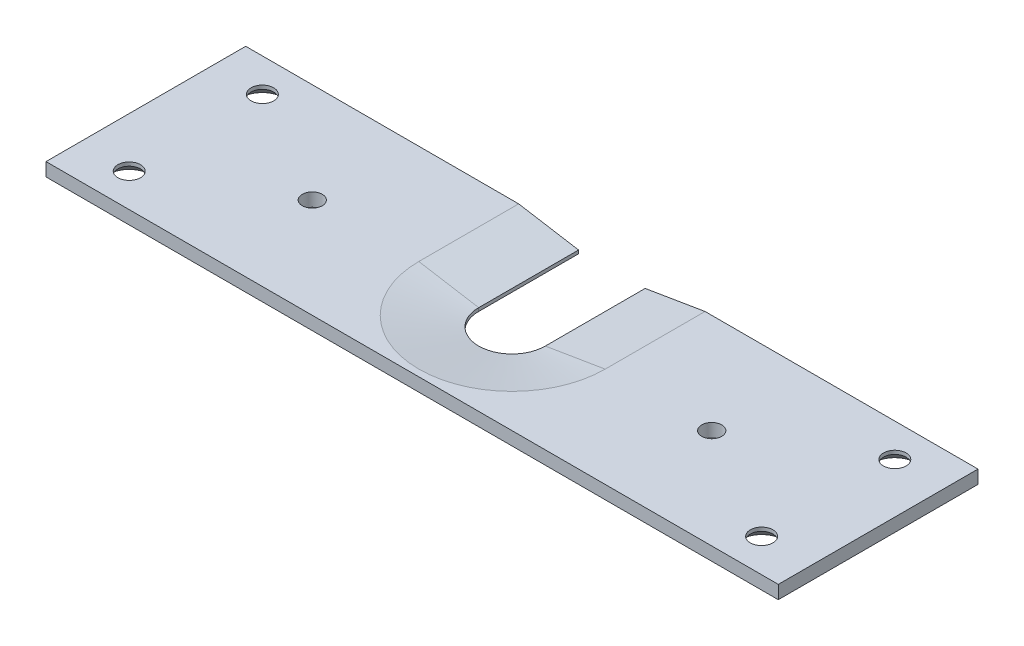
SolidWorks part; units mm, degrees
ref_plane "Front Plane" through (0, 0, 0) normal (0, 0, 1) x (1, 0, 0)
ref_plane "Top Plane" through (0, 0, 0) normal (0, 1, 0) x (1, 0, 0)
ref_plane "Right Plane" through (0, 0, 0) normal (1, 0, 0) x (0, 0, -1)
sketch "Sketch1" plane through (0, 0, 0) normal (0, 1, 0) x (1, 0, 0)
  line L1 (-55, 15) -> (55, 15)
  line L2 (-55, 15) -> (-55, -15)
  line L3 (-55, -15) -> (55, -15)
  line L4 (55, 15) -> (55, -15)
  dimension "D5" = 15
  dimension "D1" = 55
  dimension "D2" = 55
  dimension "D4" = 15
extrude "Extrude1" add sketch "Sketch1" along normal blind 2
sketch "Sketch2" plane through (0, 2, 0) normal (0, 1, 0) x (-1, 0, 0)
  line L0 (-55, -15) -> (55, -15) construction
  line L2 (5, 0) -> (5, -15)
  line L3 (5, -15) -> (-5, -15)
  line L4 (-5, 0) -> (-5, -15)
  arc A1 (5, 0) -> (-5, 0) centre (0, 0) ccw
extrude "Cut-Extrude1" cut sketch "Sketch2" against normal through all
chamfer "Chamfer1" distance 9 distance2 1.5 3 edges at (5, 2, -7.5) (0, 2, 5) (-5, 2, -7.5)
hole_wizard "CSK for M3 Countersunk Raised Head Screw1" positions "Sketch9" profile "Sketch8" countersink size "M3" standard "ISO" end condition through all
sketch "Sketch9" plane through (0, 0, 0) normal (0, -1, 0) x (1, 0, 0)
  line L0 (-55, -15) -> (-55, 15) construction
  line L1 (55, 15) -> (55, -15) construction
  line L3 (-55, 15) -> (55, 15) construction
  line L4 (55, -15) -> (5, -15) construction
  point P0 (47.5, -10)
  point P1 (-47.5, -10)
  point P4 (-47.5, 10)
  point P6 (47.5, 10)
  dimension "D1" = 7.5
  dimension "D2" = 7.5
  dimension "D3" = 5
  dimension "D4" = 5
sketch "Sketch8" plane through (47.5, 0, -10) normal (1, 0, 0) x (0, 0, -1)
  line L0 (0, 0) -> (0, 2)
  line L1 (0, 2) -> (1.7, 2)
  line L2 (1.7, 2) -> (1.7, 1.45)
  line L3 (1.7, 1.45) -> (3.15, 0)
  line L5 (3.15, 0) -> (0, 0)
  line L6 (-1.7, 1.45) -> (-3.15, 0) construction
  line L11 (0, -6.35) -> (0, 107.95) construction
  dimension "Thru Hole Dia." = 3.4
  dimension "Thru Hole Depth" = 2
  dimension "Near C'Sink Dia." = 6.3
  dimension "Near C'Sink Angle" = 90
hole_wizard "M3 Tapped Hole1" positions "Sketch11" profile "Sketch12" tap size "M3" standard "ISO" end condition through all
sketch "Sketch11" plane through (0, 2, 0) normal (0, 1, 0) x (-1, 0, 0)
  line L0 (55, 15) -> (-55, 15) construction
  line L1 (-55, 15) -> (-55, -15) construction
  line L2 (55, -15) -> (55, 15) construction
  point P5 (-30, 0)
  point P7 (30, 0)
  dimension "D1" = 15
  dimension "D2" = 25
  dimension "D3" = 25
sketch "Sketch12" plane through (30, 2, 0) normal (1, 0, 0) x (0, 0, 1)
  line L0 (0, 0) -> (0, 2)
  line L1 (0, 2) -> (1.5, 2)
  line L2 (1.5, 2) -> (1.5, 0)
  line L5 (1.5, 0) -> (0, 0)
  line L11 (0, -6.35) -> (0, 107.95) construction
  dimension "Thread Major Dia." = 3
  dimension "Thru Tap Drill Depth" = 2
sketch "Sketch13" plane through (0, 0, 0) normal (0, -1, 0) x (1, 0, 0)
  circle A0 centre (0, -32.271) radius 30.9632
equation "\"D2@Sketch1\" = \"D1@Sketch1\""
equation "\"D5@Sketch1\"=\"D4@Sketch1\""
equation "\"D2@Sketch9\" = \"D1@Sketch9\""
equation "\"D4@Sketch9\" = \"D3@Sketch9\""
equation "\"D3@Sketch11\" = \"D2@Sketch11\""
